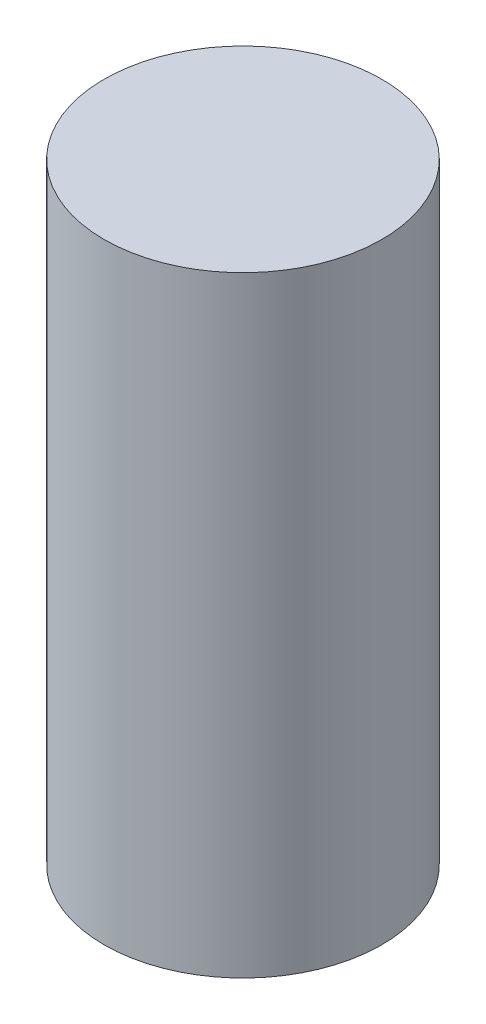
SolidWorks part; units mm, degrees
ref_plane "Front Plane" through (0, 0, 0) normal (0, 0, 1) x (1, 0, 0)
ref_plane "Top Plane" through (0, 0, 0) normal (0, 1, 0) x (1, 0, 0)
ref_plane "Right Plane" through (0, 0, 0) normal (1, 0, 0) x (0, 0, -1)
sketch "Sketch1" plane through (0, 0, 0) normal (0, 1, 0) x (1, 0, 0)
  circle A0 centre (0, 0) radius 25
extrude "Boss-Extrude1" add sketch "Sketch1" along normal blind 110
